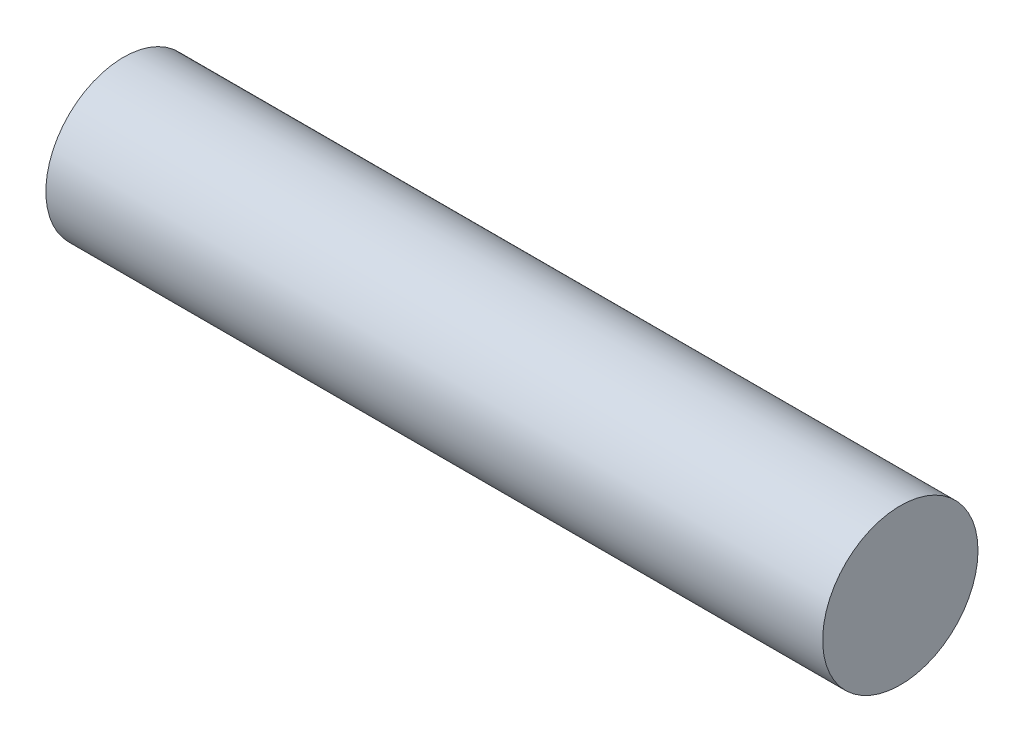
SolidWorks part; units mm, degrees
ref_plane "Front Plane" through (0, 0, 0) normal (0, 0, 1) x (1, 0, 0)
ref_plane "Top Plane" through (0, 0, 0) normal (0, 1, 0) x (1, 0, 0)
ref_plane "Right Plane" through (0, 0, 0) normal (1, 0, 0) x (0, 0, -1)
sketch "Sketch1" plane through (0, 0, 0) normal (1, 0, 0) x (0, 0, -1)
  circle A0 centre (0, 0) radius 3
extrude "Boss-Extrude1" add sketch "Sketch1" along normal blind 30
